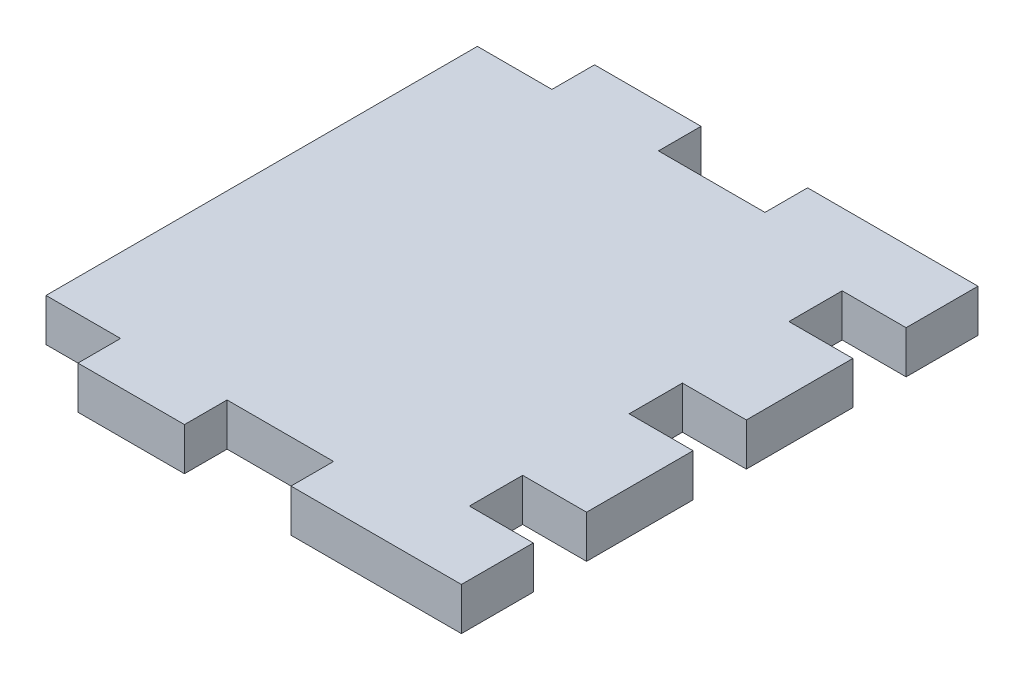
SolidWorks part; units mm, degrees
material "Maple"
ref_plane "Front Plane" through (0, 0, 0) normal (0, 0, 1) x (1, 0, 0)
ref_plane "Top Plane" through (0, 0, 0) normal (0, 1, 0) x (1, 0, 0)
ref_plane "Right Plane" through (0, 0, 0) normal (1, 0, 0) x (0, 0, -1)
sketch "Sketch1" plane through (0, 0, 0) normal (0, 1, 0) x (1, 0, 0)
  line L1 (0, 0) -> (37, 0)
  line L2 (0, 0) -> (0, -40.5)
  line L3 (0, -40.5) -> (37, -40.5)
  line L4 (37, 0) -> (37, -40.5)
  dimension "D1" = 37
  dimension "D2" = 40.5
extrude "Boss-Extrude1" add sketch "Sketch1" along normal blind 4
sketch "Sketch2" plane through (0, 0, 0) normal (0, -1, 0) x (-1, 0, 0)
  line L0 (-37, -40.5) -> (-37, 0) construction
  line L1 (-37, 0) -> (-27, 0)
  line L2 (-37, 0) -> (-37, 4)
  line L3 (-37, 4) -> (-27, 4)
  line L4 (-27, 0) -> (-27, 4)
  line L5 (-37, 0) -> (0, 0) construction
  line L6 (-37, -40.5) -> (-27, -40.5)
  line L7 (-37, -40.5) -> (-37, -44.5)
  line L8 (-37, -44.5) -> (-27, -44.5)
  line L9 (-27, -40.5) -> (-27, -44.5)
  line L10 (0, -40.5) -> (-37, -40.5) construction
  dimension "D1" = 10
  dimension "D2" = 4
  dimension "D3" = 10
  dimension "D4" = 4
extrude "Boss-Extrude2" add sketch "Sketch2" against normal through all
pattern_linear "LPattern1" count 2 spacing 20 along (-1, 0, 0) of "Boss-Extrude2"
sketch "Sketch3" plane through (37, 0, 0) normal (1, 0, 0) x (0, 0, -1)
  line L0 (4, 4) -> (4, 0) construction
  line L1 (4, 0) -> (-2.75, 0)
  line L2 (4, 0) -> (4, 4)
  line L3 (4, 4) -> (-2.75, 4)
  line L4 (-2.75, 0) -> (-2.75, 4)
  line L5 (-44.5, 0) -> (4, 0) construction
  line L6 (-44.5, 4) -> (4, 4) construction
  line L7 (-44.5, 4) -> (-44.5, 0) construction
  line L8 (-17.75, 0) -> (-7.75, 0)
  line L9 (-17.75, 0) -> (-17.75, 4)
  line L10 (-17.75, 4) -> (-7.75, 4)
  line L11 (-7.75, 0) -> (-7.75, 4)
  line L12 (-22.75, 4) -> (-32.75, 4)
  line L13 (-22.75, 4) -> (-22.75, 0)
  line L14 (-22.75, 0) -> (-32.75, 0)
  line L15 (-32.75, 4) -> (-32.75, 0)
  line L16 (-37.75, 4) -> (-44.5, 4)
  line L17 (-37.75, 4) -> (-37.75, 0)
  line L18 (-37.75, 0) -> (-44.5, 0)
  line L19 (-44.5, 4) -> (-44.5, 0)
  dimension "D1" = 6.75
  dimension "D2" = 6.75
  dimension "D3" = 5
  dimension "D4" = 5
  dimension "D5" = 10
  dimension "D6" = 10
extrude "Boss-Extrude3" add sketch "Sketch3" along normal blind 6
equation "\"D3@Sketch2\"=\"D1@Sketch2\""
equation "\"D4@Sketch2\"=\"D2@Sketch2\""
